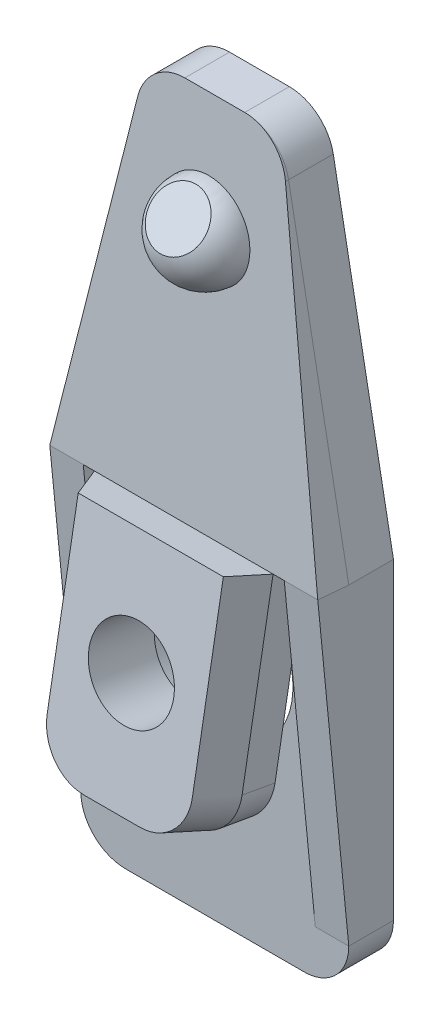
SolidWorks part; units mm, degrees
ref_plane "Front Plane" through (0, 0, 0) normal (0, 0, 1) x (1, 0, 0)
ref_plane "Top Plane" through (0, 0, 0) normal (0, 1, 0) x (1, 0, 0)
ref_plane "Right Plane" through (0, 0, 0) normal (1, 0, 0) x (0, 0, -1)
sketch "Sketch1" plane through (0, 0, 0) normal (0, 0, 1) x (1, 0, 0)
  line L0 (0, 0) -> (0, -10486.1436) construction
  line L1 (-4, -10) -> (4, -10)
  line L2 (6, -8) -> (6, 6)
  line L3 (6, 6) -> (3.3059, 20.3686)
  line L4 (1.3401, 22) -> (-1.3401, 22)
  line L5 (-6, 6) -> (-3.3059, 20.3686)
  line L6 (-6, -8) -> (-6, 6)
  arc A0 (3.3059, 20.3686) -> (1.3401, 22) centre (1.3401, 20) ccw
  arc A1 (4, -10) -> (6, -8) centre (4, -8) ccw
  arc A2 (-4, -10) -> (-6, -8) centre (-4, -8) cw
  arc A3 (-3.3059, 20.3686) -> (-1.3401, 22) centre (-1.3401, 20) cw
  point P3 (-6, -10)
  point P10 (3, 22)
  point P13 (6, -10)
  point P21 (0, 22)
  point P22 (0, -10)
  point P23 (-3, 22)
  dimension "D5" = 2
  dimension "D1" = 3
  dimension "D2" = 6
  dimension "D3" = 32
  dimension "D4" = 16
  dimension "10" = 10
extrude "Boss-Extrude1" add sketch "Sketch1" along normal blind 2
sketch "Sketch8" plane through (0, 0, 0) normal (0, 0, -1) x (-1, 0, 0)
  line L0 (-4, -4) -> (4, -4)
  line L2 (4, -5.5) -> (-4, -5.5)
  line L3 (-6, -8) -> (-6, 6) construction
  line L4 (6, 6) -> (6, -8) construction
  line L5 (4, -10) -> (-4, -10) construction
  line L6 (-4, -7) -> (4, -7)
  line L8 (4, -8.5) -> (-4, -8.5)
  arc A0 (-4, -4) -> (-4, -5.5) centre (-4, -4.75) ccw
  arc A1 (4, -5.5) -> (4, -4) centre (4, -4.75) ccw
  arc A2 (-4, -7) -> (-4, -8.5) centre (-4, -7.75) ccw
  arc A3 (4, -8.5) -> (4, -7) centre (4, -7.75) ccw
  dimension "D3" = 1.5
  dimension "D5" = 0.75
  dimension "D1" = 2
  dimension "D2" = 2
  dimension "D4" = 4.5
  dimension "D6" = 1.5
extrude "FingerGrip" cut sketch "Sketch8" against normal blind 0.3
ref_plane "Plane1" through (0, 0.3408, 3.8949) normal (0, 0.0872, 0.9962) x (-1, 0, 0)
sketch "Sketch2" plane through (0, 0.3408, 3.8949) normal (0, 0.0872, 0.9962) x (-1, 0, 0)
  line L3 (6, -5.8029) -> (-6, -5.8029)
  line L6 (-1.3401, -21.742) -> (1.3401, -21.742)
  line L7 (3.3059, -20.1168) -> (6, -5.8029)
  line L8 (6, -5.8029) -> (6, 8.1439)
  line L9 (4, 10.1363) -> (-4, 10.1363)
  line L10 (-6, 8.1439) -> (-6, -5.8029)
  line L11 (-6, -5.8029) -> (-3.3059, -20.1168)
  line L12 (-1.3401, -21.742) -> (1.3401, -21.742)
  line L13 (3.3059, -20.1168) -> (6, -5.8029)
  line L17 (-6, -5.8029) -> (-3.3059, -20.1168)
  ellipse E4 centre (-1.3401, -19.7496) end of major axis (0.6599, -19.7496) minor radius 1.9924 (-3.3059, -20.1168) -> (-1.3401, -21.742) ccw
  ellipse E5 centre (1.3401, -19.7496) end of major axis (3.3401, -19.7496) minor radius 1.9924 (1.3401, -21.742) -> (3.3059, -20.1168) ccw
  ellipse E6 centre (4, 8.1439) end of major axis (6, 8.1439) minor radius 1.9924 (6, 8.1439) -> (4, 10.1363) ccw
  ellipse E7 centre (-4, 8.1439) end of major axis (-2, 8.1439) minor radius 1.9924 (-4, 10.1363) -> (-6, 8.1439) ccw
  ellipse E8 centre (-1.3401, -19.7496) end of major axis (0.6599, -19.7496) minor radius 1.9924 (-3.3059, -20.1168) -> (-1.3401, -21.742) ccw
  ellipse E9 centre (1.3401, -19.7496) end of major axis (3.3401, -19.7496) minor radius 1.9924 (1.3401, -21.742) -> (3.3059, -20.1168) ccw
  point P3 (4.3725, -5.5616)
  point P11 (0, 0)
  point P14 (0, 0)
  point P15 (5.7796, -5.8029)
  dimension "width" = 12
  dimension "D1" = 0
extrude "Boss-Extrude2" add sketch "Sketch2" against normal blind 2
sketch "Sketch9" plane through (0, 0.3408, 3.8949) normal (0, 0.0872, 0.9962) x (1, 0, 0)
  line L0 (1.3401, 21.742) -> (-1.3401, 21.742) construction
  line L1 (0, 16.742) -> (50000, 16.742) construction
  line L2 (-2, 16.742) -> (2, 16.742)
  circle A0 centre (0, 16.742) radius 2 construction
  arc A1 (-2, 16.742) -> (2, 16.742) centre (0, 16.742) ccw
  dimension "D1" = 4
  dimension "D2" = 5
revolve "Revolve1" add sketch "Sketch9" angle 180 about L1
sketch "Sketch11" plane through (0, 0, 0) normal (1, 0, 0) x (0, 0, -1)
  line L0 (-4.4352, 17.0658) -> (-2.8473, 18.9762)
  line L1 (-2.8473, 18.9762) -> (-5.7551, 18.9762)
  line L2 (-5.7551, 18.9762) -> (-4.4352, 17.0658)
  arc A0 (-2.2615, 19.0114) -> (-2.6101, 15.0266) centre (-2.4358, 17.019) ccw construction
extrude "Cut-Extrude3" cut sketch "Sketch11" against normal through all both and the other way through all
ref_plane "Plane4" through (0, 0.7642, 4.3338) normal (0, 0.1736, 0.9848) x (1, 0, 0)
sketch "Sketch17" plane through (0, 0.7642, 4.3338) normal (0, 0.1736, 0.9848) x (1, 0, 0)
  line L0 (0, -1.1) -> (0, 1.1) construction
  line L1 (-4, 7.44) -> (-4, -2.56)
  line L3 (-2, -4.56) -> (2, -4.56)
  line L4 (4, -2.56) -> (4, 7.44)
  line L6 (-6, 5.44) -> (6, 5.44) construction
  line L7 (-4, 7.44) -> (4, 7.44)
  circle A0 centre (0, 0.44) radius 1.9 construction
  circle A1 centre (0, 0.44) radius 3.5 construction
  arc A2 (-4, -2.56) -> (-2, -4.56) centre (-2, -2.56) ccw
  arc A3 (2, -4.56) -> (4, -2.56) centre (2, -2.56) ccw
  point P9 (0, 0)
  point P10 (0, 5.44)
  point P14 (0, 7.44)
  point P15 (0, 0)
  point P17 (-4, -4.56)
  point P20 (4, -4.56)
  dimension "D1" = 3.8
  dimension "D2" = 7
  dimension "D5" = 2
  dimension "D3" = 12
  dimension "D4" = 8
  dimension "D6" = 2
  dimension "D7" = 5
extrude "Boss-Extrude6" add sketch "Sketch17" against normal blind 1.5
ref_plane "Plane5" through (0, 1.0246, 5.811) normal (0, 0.1736, 0.9848) x (1, 0, 0)
sketch "Sketch23" plane through (0, 0.7642, 4.3338) normal (0, 0.1736, 0.9848) x (1, 0, 0)
  line L1 (-4, 5.44) -> (-4, -2.56)
  line L2 (-6, 5.44) -> (6, 5.44) construction
  line L3 (-2, -4.56) -> (2, -4.56)
  line L4 (4, -2.56) -> (4, 5.44)
  line L7 (-4, 5.44) -> (4, 5.44)
  arc A2 (-4, -2.56) -> (-2, -4.56) centre (-2, -2.56) ccw
  arc A3 (2, -4.56) -> (4, -2.56) centre (2, -2.56) ccw
  point P3 (0, 0)
  point P4 (0, -4.56)
  point P9 (0, 0)
  point P17 (-4, -4.56)
  point P20 (4, -4.56)
  dimension "D5" = 2
  dimension "D3" = 10
  dimension "D4" = 8
sketch "Sketch19" plane through (0, 1.0246, 5.811) normal (0, 0.1736, 0.9848) x (1, 0, 0)
  line L0 (-3.25, 5.44) -> (-3.25, -2.56)
  line L2 (-1.25, -4.56) -> (1.25, -4.56)
  line L3 (3.25, -2.56) -> (3.25, 5.44)
  line L4 (3.25, 5.44) -> (-3.25, 5.44)
  line L5 (-6, 5.44) -> (6, 5.44) construction
  arc A0 (1.25, -4.56) -> (3.25, -2.56) centre (1.25, -2.56) ccw
  arc A1 (-3.25, -2.56) -> (-1.25, -4.56) centre (-1.25, -2.56) ccw
  point P2 (-3.0522, 5.44)
  point P7 (2.9602, 5.44)
  point P8 (0, -4.56)
  point P9 (0, 5.44)
  point P13 (3.25, -4.56)
  point P16 (-3.25, -4.56)
  dimension "D3" = 2
  dimension "D1" = 6.5
  dimension "D2" = 10
loft "ChannelLoft" add profiles "Sketch23", "Sketch19"
sketch "Sketch24" plane through (0, 1.0246, 5.811) normal (0, 0.1736, 0.9848) x (1, 0, 0)
  circle A0 centre (0, 0.44) radius 1.9
  dimension "D1" = 3.8
extrude "Screw Threads" cut sketch "Sketch24" against normal up to surface (3 mm away) up to face at (0, -0.3502, 3.0072)
sketch "Sketch25" plane through (0, 0.5037, 2.8566) normal (0, -0.1736, -0.9848) x (-1, 0, 0)
  circle A0 centre (0, 0.44) radius 3.5
  dimension "D1" = 7
extrude "Screw Head" cut sketch "Sketch25" along normal up to surface (2.206 mm away)
sketch "Sketch26" plane through (6, 0, 0) normal (1, 0, 0) x (0, 0, -1)
  line L0 (-2, 6) -> (-3.3892, 6.1215)
  line L1 (-3.3892, 6.1215) -> (-2.1416, 20.381) construction
  line L2 (-2, 6) -> (-3.3892, 6.1215) construction
  line L3 (-3.3892, 6.1215) -> (-2, -8)
  line L4 (-2, -8) -> (-2, 6)
extrude "Wall1" add sketch "Sketch26" against normal blind 1.5
sketch "Sketch27" plane through (-6, 0, 0) normal (-1, 0, 0) x (0, 0, 1)
  line L0 (3.3892, 6.1215) -> (2, 6)
  line L1 (3.3892, 6.1215) -> (2.1416, 20.381) construction
  line L2 (2.1416, 20.381) -> (3.3892, 6.1215) construction
  line L3 (2, 6) -> (2, -8)
  line L4 (2, -8) -> (3.3892, 6.1215)
extrude "Wall2" add sketch "Sketch27" against normal blind 1.5
